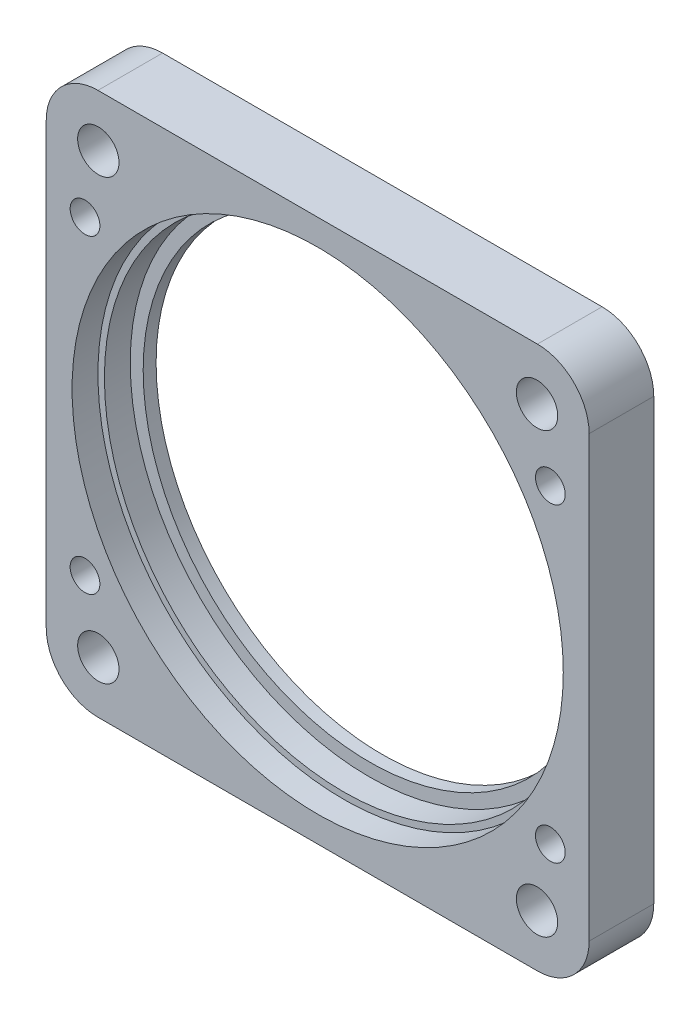
SolidWorks part; units mm, degrees
ref_plane "前视基准面" through (0, 0, 0) normal (0, 0, 1) x (1, 0, 0)
ref_plane "上视基准面" through (0, 0, 0) normal (0, 1, 0) x (1, 0, 0)
ref_plane "右视基准面" through (0, 0, 0) normal (1, 0, 0) x (0, 0, -1)
sketch "草图1" plane through (0, 0, 0) normal (0, 0, 1) x (1, 0, 0)
  line L1 (-21, 21) -> (21, 21)
  line L2 (-21, 21) -> (-21, -21)
  line L3 (-21, -21) -> (21, -21)
  line L4 (21, 21) -> (21, -21)
  line L5 (0, -21) -> (0, 21) construction
  line L6 (-21, 0) -> (21, 0) construction
  point P0 (0, 0)
  dimension "D1" = 42
  dimension "D2" = 42
extrude "凸台-拉伸1" add sketch "草图1" along normal blind 5
sketch "草图2" plane through (0, 0, 5) normal (0, 0, 1) x (1, 0, 0)
  circle A0 centre (0, 0) radius 17.5
  dimension "D1" = 35
extrude "切除-拉伸1" cut sketch "草图2" against normal through all
sketch "草图3" plane through (0, 0, 5) normal (0, 0, 1) x (1, 0, 0)
  circle A0 centre (0, 0) radius 18.5
  dimension "D1" = 37
extrude "切除-拉伸2" cut sketch "草图3" against normal offset from surface (4 mm away) 1 up to face at (17.5, 0, 0)
sketch "草图4" plane through (0, 0, 5) normal (0, 0, 1) x (1, 0, 0)
  circle A0 centre (0, 0) radius 19
  dimension "D1" = 38
extrude "切除-拉伸3" cut sketch "草图4" against normal offset from surface (2 mm away) 2 contours A0 up to face at (18.5, 0, 1)
fillet "圆角1" radius 4 4 edges at (-21, -21, 2.5) (21, -21, 2.5) (21, 21, 2.5) (-21, 21, 2.5)
sketch "草图5" plane through (0, 0, 5) normal (0, 0, 1) x (1, 0, 0)
  circle A0 centre (-16.9706, 16.9706) radius 1.6
  circle A3 centre (16.9706, 16.9706) radius 1.6
  circle A4 centre (16.9706, -16.9706) radius 1.6
  circle A5 centre (-16.9706, -16.9706) radius 1.6
  point P12 (0, 0)
  dimension "D1" = 3.2
  dimension "D2" = 24
  dimension "D4" = 4
sketch "草图6" plane through (0, 0, 5) normal (0, 0, 1) x (1, 0, 0)
  line L0 (-21, 17) -> (-21, -17) construction
  line L2 (-21, -9) -> (-21, -13)
  line L3 (-21, -13) -> (-17, -13)
  line L5 (-21, -9) -> (-17, -13)
  line L6 (-17, -21) -> (17, -21) construction
  line L7 (-9, 21) -> (-13, 17)
  line L8 (-13, 21) -> (-13, 17)
  line L9 (-9, 21) -> (-13, 21)
  line L10 (21, 9) -> (17, 13)
  line L11 (21, 13) -> (17, 13)
  line L12 (21, 9) -> (21, 13)
  line L13 (9, -21) -> (13, -17)
  line L14 (13, -21) -> (13, -17)
  line L15 (9, -21) -> (13, -21)
  point P19 (0, 0)
  dimension "D1" = 4
  dimension "D2" = 4
  dimension "D3" = 8
  dimension "D4" = 4
extrude "凸台-拉伸2" [suppressed] add sketch "草图6" along normal blind 3
pattern_circular "阵列(圆周)1" [suppressed] count 4 over 360
extrude "切除-拉伸4" cut sketch "草图5" against normal through all
sketch "草图7" plane through (0, 0, 0) normal (0, 0, -1) x (-1, 0, 0)
  line L0 (-21, -17) -> (-21, 17) construction
  line L1 (-17, 21) -> (17, 21) construction
  line L2 (-28.4314, 0) -> (27.643, 0) construction
  line L4 (0, 29.0062) -> (0, -29.8069) construction
  circle A0 centre (-18, 12) radius 1.15
  circle A4 centre (18, 12) radius 1.15
  circle A5 centre (18, -12) radius 1.15
  circle A6 centre (-18, -12) radius 1.15
  dimension "D1" = 2.3
  dimension "D2" = 3
  dimension "D3" = 9
extrude "切除-拉伸5" cut sketch "草图7" against normal through all
sketch "草图8" plane through (0, 0, 0) normal (0, 0, -1) x (-1, 0, 0)
  line L2 (-28.4314, 0) -> (27.643, 0) construction
  line L3 (-28.4314, 0) -> (27.643, 0) construction
  line L4 (0, 29.0062) -> (0, -29.8069) construction
  line L5 (0, 29.0062) -> (0, -29.8069) construction
  circle A0 centre (-18, 12) radius 2
  circle A1 centre (18, 12) radius 2
  circle A2 centre (18, -12) radius 2
  circle A3 centre (-18, -12) radius 2
  dimension "D1" = 4
extrude "切除-拉伸6" cut sketch "草图8" against normal blind 3
